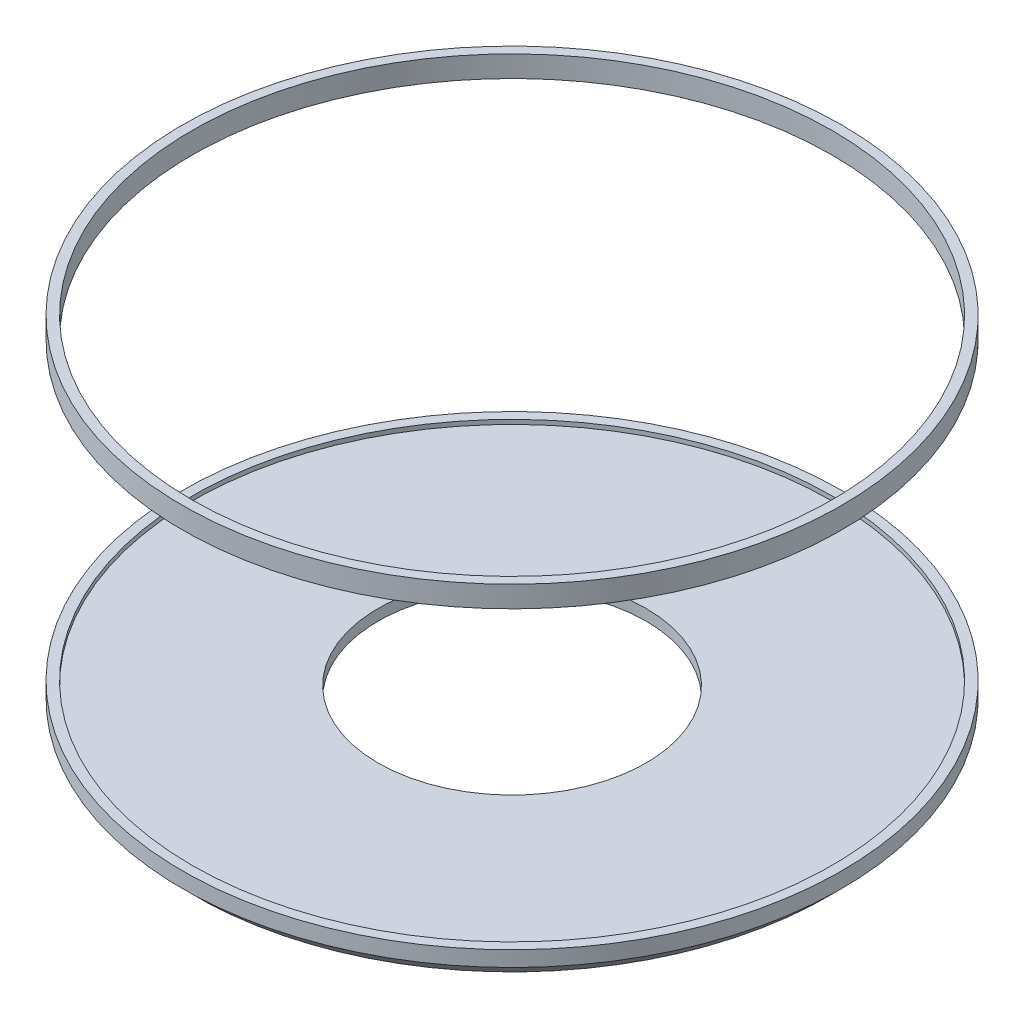
SolidWorks part; units mm, degrees
ref_plane "Alzado" through (0, 0, 0) normal (0, 0, 1) x (1, 0, 0)
ref_plane "Planta" through (0, 0, 0) normal (0, 1, 0) x (1, 0, 0)
ref_plane "Vista lateral" through (0, 0, 0) normal (1, 0, 0) x (0, 0, -1)
sketch "Croquis1" plane through (0, 0, 0) normal (1, 0, 0) x (0, 0, -1)
  line L0 (0, 0) -> (0, -66.5134) construction
  line L1 (0, -66.5134) -> (0, 82.3614) construction
  line L2 (54.2673, -66.5134) -> (128.2245, -66.5134)
  line L3 (128.2245, -66.5134) -> (128.2245, -60.2703)
  line L4 (128.2245, -60.2703) -> (128.2245, 59.3098)
  line L5 (128.2245, 59.3098) -> (133.5071, 59.3098)
  line L6 (133.5071, 59.3098) -> (133.5071, 67.9542)
  line L7 (133.5071, 67.9542) -> (54.2673, 67.9542)
  line L8 (54.2673, 67.9542) -> (54.2673, -66.5134)
  line L9 (128.2245, -60.2703) -> (133.5071, -60.2703)
  line L10 (133.5071, -60.2703) -> (133.5071, -66.5134)
  line L11 (133.5071, -66.5134) -> (128.2245, -71.7961)
  line L12 (128.2245, -71.7961) -> (128.2245, -60.2703)
revolve "Revolución1" add sketch "Croquis1" angle 360 about L1
sketch "Croquis2" plane through (0, 67.9542, 0) normal (0, 1, 0) x (1, 0, 0)
  circle A0 centre (0, 0) radius 129.6279
extrude "Cortar-Extruir1" cut sketch "Croquis2" against normal blind 130
